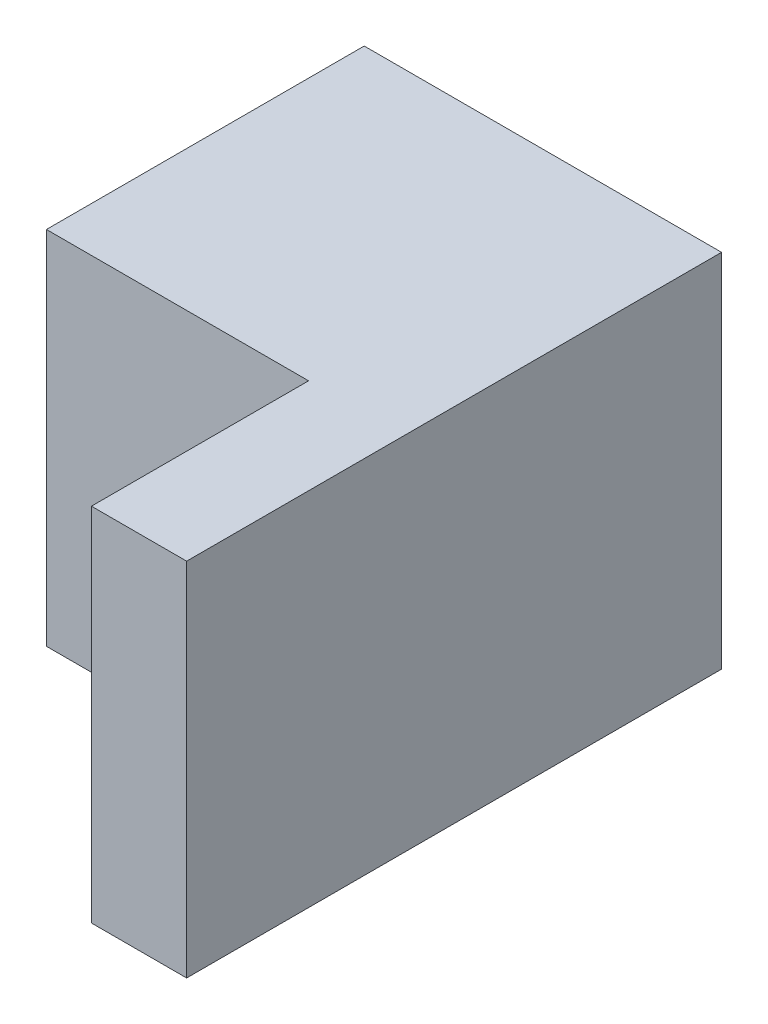
SolidWorks part; units mm, degrees
ref_plane "Front Plane" through (0, 0, 0) normal (0, 0, 1) x (1, 0, 0)
ref_plane "Top Plane" through (0, 0, 0) normal (0, 1, 0) x (1, 0, 0)
ref_plane "Right Plane" through (0, 0, 0) normal (1, 0, 0) x (0, 0, -1)
sketch "Sketch1" plane through (0, 0, 0) normal (0, 0, 1) x (1, 0, 0)
  line L1 (-33.735, -34.0815) -> (33.735, -34.0815)
  line L2 (-33.735, -34.0815) -> (-33.735, 34.0815)
  line L3 (-33.735, 34.0815) -> (33.735, 34.0815)
  line L4 (33.735, -34.0815) -> (33.735, 34.0815)
  line L5 (-33.735, -34.0815) -> (33.735, 34.0815) construction
  line L6 (-33.735, 34.0815) -> (33.735, -34.0815) construction
  point P0 (0, 0)
extrude "Boss-Extrude1" add sketch "Sketch1" along normal blind 60
sketch "Sketch2" plane through (0, 0, 60) normal (0, 0, 1) x (1, 0, 0)
  line L0 (33.735, 34.0815) -> (-33.735, 34.0815) construction
  line L1 (15.7596, 34.0815) -> (33.735, 34.0815)
  line L2 (15.7596, 34.0815) -> (15.7596, -34.0815)
  line L3 (15.7596, -34.0815) -> (33.735, -34.0815)
  line L4 (33.735, 34.0815) -> (33.735, -34.0815)
extrude "Boss-Extrude2" add sketch "Sketch2" along normal blind 41
